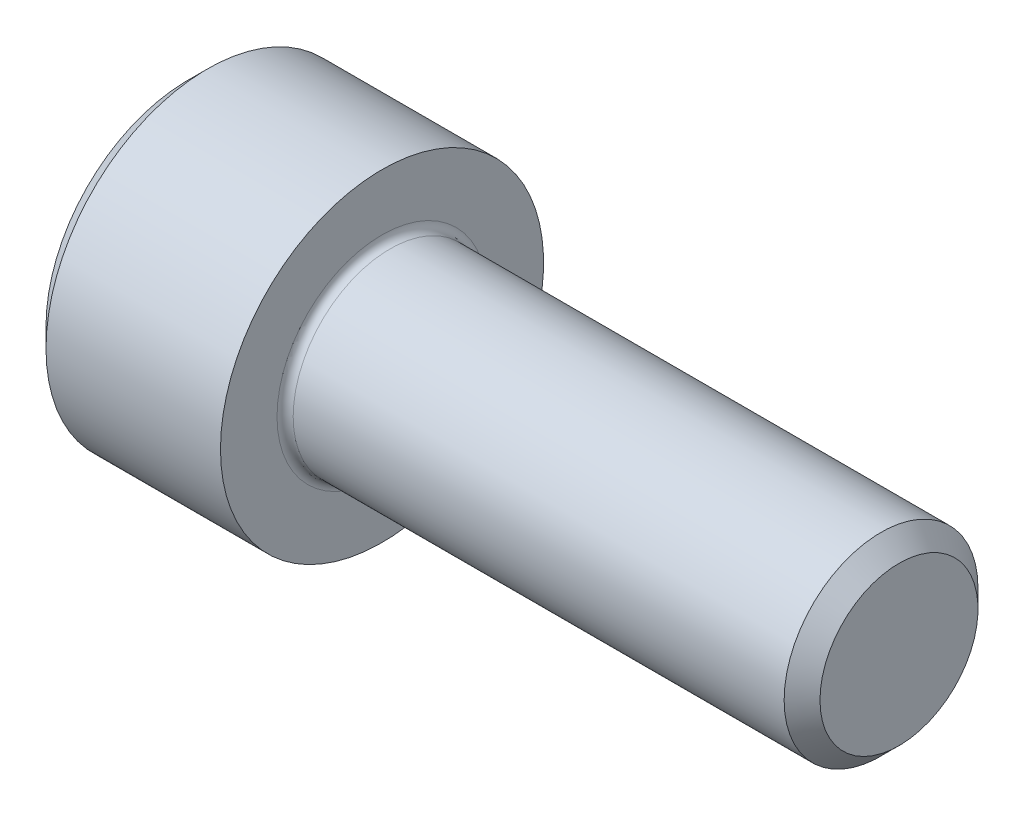
SolidWorks part; units mm, degrees
revolve "Base-Revolve" add sketch "BodySke"
sketch "BodySke" plane through (0, 0, 0) normal (0, 0, 1) x (1, 0, 0)
  line L0 (0, 0) -> (0, 4.4)
  line L1 (0.6, 5) -> (6, 5)
  line L2 (6, 5) -> (6, 3)
  line L3 (6, 3) -> (21.4455, 3)
  line L4 (22, 2.4455) -> (22, 0)
  line L5 (22, 0) -> (0, 0)
  line L6 (-31.75, 0) -> (127, 0) construction
  line L7 (0, 4.4) -> (0.6, 5)
  line L8 (22, 2.4455) -> (21.4455, 3)
  line L9 (0, -4.4) -> (0.6, -5) construction
  line L10 (22, -2.4455) -> (21.4455, -3) construction
  line L11 (7, 9.525) -> (7, 3.175) construction
  line L12 (6, 9.525) -> (6, 3.175) construction
  line L13 (-28, 9.525) -> (-28, 3.175) construction
  dimension "Diameter" = 6
  dimension "Head_ht" = 6
  dimension "Length" = 16
  dimension "Body_ch_ang" = 45
  dimension "Head_dia" = 10
  dimension "Head_ch_ang" = 45
  dimension "Minor_dia" = 4.891
  dimension "Advance" = 1
  dimension "Thread_nom" = 16
  dimension "Thread_length" = 50
  dimension "Head_ch_ht" = 0.6
cosmetic thread "ThreadCosmetic" [suppressed]
fillet "Fillet1" radius 0.25 1 edges at (6, 0, 3)
ref_plane "Plane1" through (0, 0, 0) normal (0, 0, 1) x (1, 0, 0)
ref_plane "Plane2" through (0, 0, 0) normal (0, 1, 0) x (1, 0, 0)
ref_plane "Plane3" through (0, 0, 0) normal (1, 0, 0) x (0, 0, -1)
sketch "Sketch2" plane through (0, 0, 0) normal (0, 0, 1) x (1, 0, 0)
  line L0 (0, 2.542) -> (3, 2.542)
  line L1 (3, 2.542) -> (4.4676, 0)
  line L2 (-31.75, 0) -> (127, 0) construction
  line L3 (4.4676, 0) -> (0, 0)
  line L4 (0, 0) -> (0, 2.542)
  line L5 (0, 4.4) -> (0, -4.4) construction
  line L6 (0, 0) -> (47.625, 0) construction
  line L7 (6, -5) -> (6, 5) construction
  dimension "D1" = 2.542
  dimension "D2" = 60
revolve "Hex-PreBroach" cut sketch "Sketch2" angle 360 about L6
sketch "Sketch3" plane through (0, 0, 0) normal (-1, 0, 0) x (0, 0.5, 0.866)
  line L0 (1.4676, 2.542) -> (-1.4676, 2.542)
  line L1 (-1.4676, 2.542) -> (-2.9352, 0)
  line L2 (1.4676, 2.542) -> (2.9352, 0)
  line L3 (1.4676, -2.542) -> (2.9352, 0)
  line L4 (1.4676, -2.542) -> (-1.4676, -2.542)
  line L5 (-1.4676, -2.542) -> (-2.9352, 0)
  dimension "D1" = 2.542
  dimension "D2" = 2.542
  dimension "Hex_size" = 5.084
extrude "Hex" cut sketch "Sketch3" against normal blind 3
sketch "Sketch4" plane through (0, 0, 0) normal (-1, 0, 0) x (0, 0, 1)
  line L0 (0, 0) -> (2.8067, 0)
  line L1 (0, 0) -> (6.1484, 3.5498) construction
  line L2 (0, 0) -> (1.4033, 2.4307)
  line L3 (2.3336, 0.614) -> (2.6851, 0.817)
  line L4 (1.6986, 1.7139) -> (2.0501, 1.9169)
  arc A0 (2.3336, 0.614) -> (1.6986, 1.7139) centre (0, 0) ccw
  arc A1 (2.8067, 0) -> (2.6851, 0.817) centre (0, 0) ccw
  arc A2 (1.4033, 2.4307) -> (2.0501, 1.9169) centre (0, 0) cw
  dimension "D1" = 30
  dimension "D2" = 60
  dimension "Spline_p_dim" = 1.27
  dimension "D3" = 0.635
extrude "Spline" [suppressed] cut sketch "Sketch4" against normal blind 3
pattern_circular "CirPattern1" [suppressed] count 6 every 60
sketch "Sketch5" plane through (0, 0, 0) normal (0, 0, 1) x (1, 0, 0)
  line L0 (-31.75, 0) -> (127, 0) construction
  line L2 (0, 4.4) -> (0, -4.4) construction
  circle A0 centre (2.3, 0) radius 0.675
  dimension "Drilled_hole_dia" = 1.35
  dimension "Drilled_hole_loc" = 2.3
extrude "Hole" [suppressed] cut sketch "Sketch5" against normal through all and the other way through all
pattern_circular "Drilled-4" [suppressed] count 2 every 60
pattern_circular "Drilled-6" [suppressed] count 3 every 60
sketch "ThdSchSke" plane through (0, 0, 0) normal (0, 0, 1) x (1, 0, 0)
  line L0 (7, -2.4455) -> (6.6117, -3)
  line L1 (7, -2.4455) -> (7.3883, -3)
  line L2 (7.3883, -3) -> (7.3883, -3.75)
  line L3 (-3.175, 0) -> (5.1513, 0) construction
  line L5 (7.3883, -3.75) -> (6.6117, -3.75)
  line L6 (6.6117, -3.75) -> (6.6117, -3)
  line L7 (0, 4.4) -> (0, -4.4) construction
  dimension "Thread_minor" = 4.891
  dimension "Diameter" = 6
  dimension "Start" = 7
revolve "ThreadSchematic" [suppressed] cut sketch "ThdSchSke" angle 360 about L3
pattern_linear "ThdSchPat" [suppressed]
equation "\"D2@Sketch3\" = \"Hex_size@Sketch3\" / 2"
equation "\"D1@Sketch3\" = \"Hex_size@Sketch3\" / 2"
equation "\"D1@Sketch2\" = \"Hex_size@Sketch3\" / 2"
equation "\"D3@Sketch4\" = \"Spline_p_dim@Sketch4\" / 2"
equation "\"Thread_minor@ThreadCosmetic\"  =  \"Minor_dia@BodySke\""
equation "\"D2@CirPattern1\" = 360 / \"Num_teeth@CirPattern1\""
equation "\"Wall_thickness@Sketch2\" = \"Head_ht@BodySke\" - \"Key_eng@Hex\""
equation "\"Thread_length@ThreadCosmetic\" = ((sgn( (\"Length@BodySke\" - \"Advance@BodySke\" ) - \"Thread_nom@BodySke\" )-1)*( (\"Length@BodySke\" - \"Advance@BodySke\" ) - \"Thread_nom@BodySke\" ))/-2+ \"Thread_nom@BodySke\""
equation "\"Thread_minor@ThdSchSke\" = \"Minor_dia@BodySke\""
equation "\"Diameter@ThdSchSke\" = \"Diameter@BodySke\""
equation "\"Overcut@ThdSchSke\" = \"Diameter@BodySke\" * 1.25"
equation "\"Start@ThdSchSke\" = \"Head_ht@BodySke\" + \"Length@BodySke\" - \"Thread_length@ThreadCosmetic\"  '---Non-countersunk---"
equation "\"Num_threads@ThdSchPat\" = int( \"Thread_length@ThreadCosmetic\" / \"Advance@BodySke\" + 0.999 )  + 1"
equation "\"Advance@ThdSchPat\" = \"Thread_length@ThreadCosmetic\" /  (\"Num_threads@ThdSchPat\" - 1) 'relax it"
equation "\"Num_threads@ThdSchPat\" = \"Num_threads@ThdSchPat\" - sgn( \"Num_threads@ThdSchPat\" - 1) '---chamfered tips only---"
